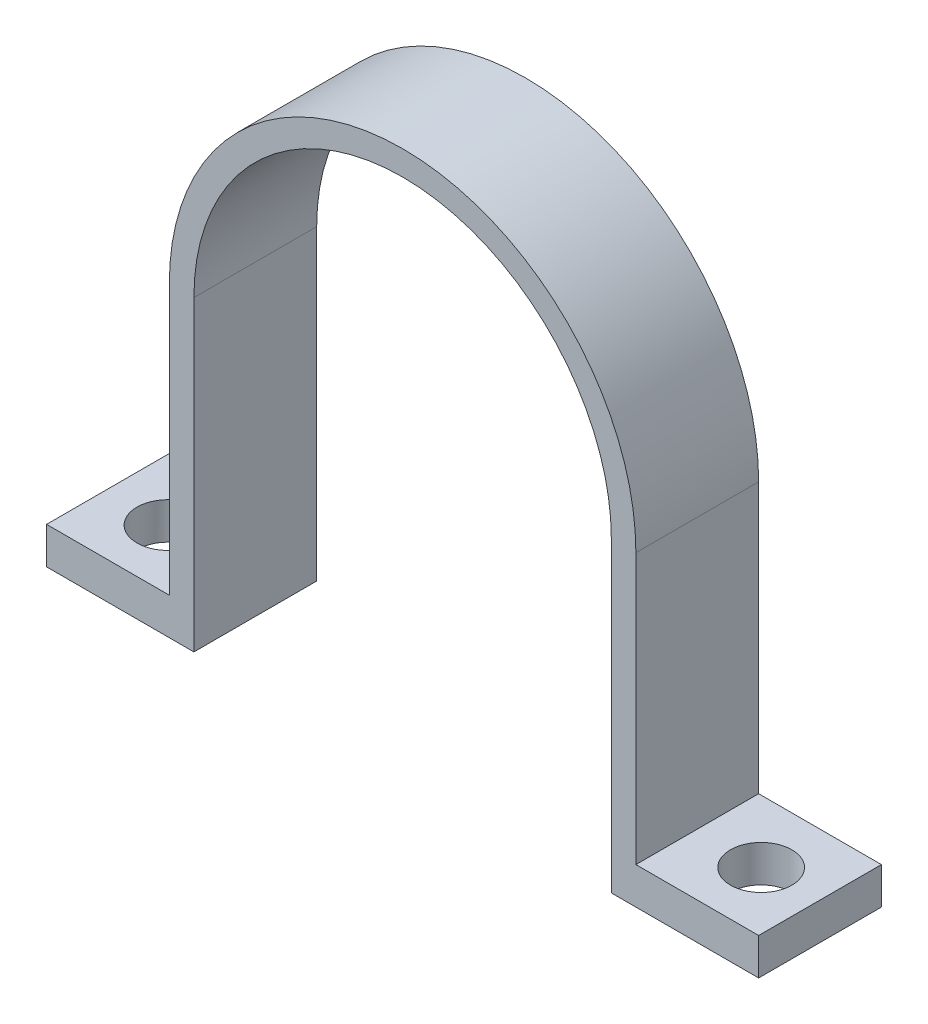
SolidWorks part; units mm, degrees
ref_plane "Front Plane" through (0, 0, 0) normal (0, 0, 1) x (1, 0, 0)
ref_plane "Top Plane" through (0, 0, 0) normal (0, 1, 0) x (1, 0, 0)
ref_plane "Right Plane" through (0, 0, 0) normal (1, 0, 0) x (0, 0, -1)
sketch "Sketch1" plane through (0, 0, 0) normal (0, 0, 1) x (1, 0, 0)
  line L0 (-17, 0) -> (-17, -24)
  line L1 (17, 0) -> (17, -24)
  line L2 (-29, -25) -> (-17, -25)
  line L5 (29, -22) -> (29, -25)
  line L6 (-17, -25) -> (-17, -24)
  line L7 (17, -24) -> (17, -25)
  line L9 (-19, 0) -> (-19, -22)
  line L10 (-29, -22) -> (-19, -22)
  line L11 (-29, -25) -> (-29, -22)
  line L12 (17.01, -29.66) -> (29, -29.66) construction
  line L13 (29, -22) -> (29, -29.66) construction
  line L14 (17, -25) -> (29, -25)
  line L16 (19, -22) -> (29, -22)
  line L17 (19, 0) -> (19, -22)
  line L20 (-29, -30) -> (-29, -22) construction
  line L21 (-16.99, -30) -> (-29, -30) construction
  line L22 (-16.99, -30) -> (17.01, -29.66) construction
  line L23 (-17, -28) -> (17, -27.66) construction
  line L24 (-17, -28) -> (-27, -28) construction
  line L25 (17, -27.66) -> (27, -27.66) construction
  line L27 (17, -24) -> (27, -24) construction
  line L28 (27, -24) -> (27, -27.66) construction
  line L29 (-27, -24) -> (-17, -24) construction
  line L30 (-27, -28) -> (-27, -24) construction
  arc A0 (17, 0) -> (-17, 0) centre (0, 0) ccw
  arc A1 (19, 0) -> (-19, 0) centre (0, 0) ccw
  point P3 (0, -25)
  point P24 (-23, -25)
  dimension "D1" = 34
  dimension "D2" = 25
  dimension "D3" = 3
  dimension "D4" = 3
  dimension "D5" = 0
  dimension "D7" = 0
  dimension "D6" = 2
extrude "Boss-Extrude1" add sketch "Sketch1" along normal blind 10
sketch "Sketch2" plane through (0, -22, 0) normal (0, 1, 0) x (1, 0, 0)
  line L0 (-29, -10) -> (-29, 0) construction
  circle A0 centre (-24, -5.101) radius 2.5349
  circle A1 centre (24.3049, -5.101) radius 2.5
  dimension "D1" = 5
  dimension "D2" = 5
extrude "Cut-Extrude1" cut sketch "Sketch2" against normal blind 10
